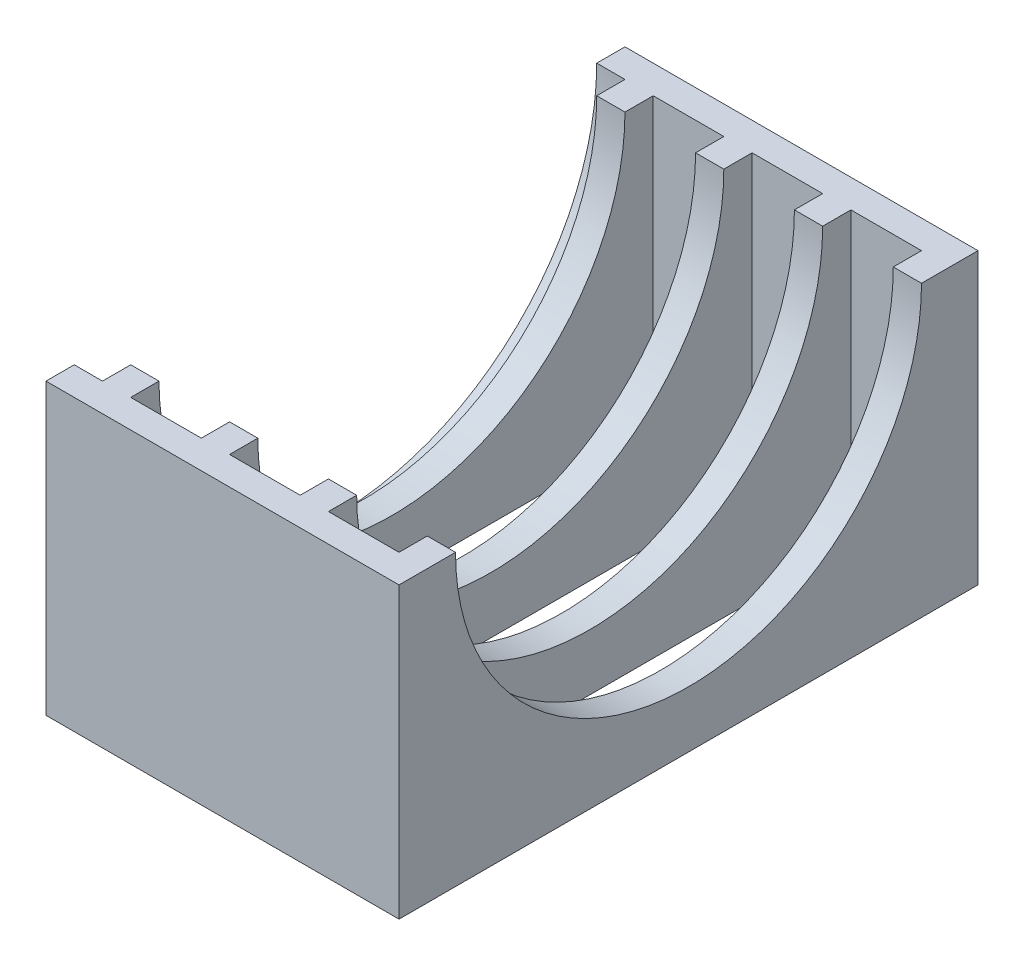
SolidWorks part; units mm, degrees
ref_plane "前视基准面" through (0, 0, 0) normal (0, 0, 1) x (1, 0, 0)
ref_plane "上视基准面" through (0, 0, 0) normal (0, 1, 0) x (1, 0, 0)
ref_plane "右视基准面" through (0, 0, 0) normal (1, 0, 0) x (0, 0, -1)
sketch "草图1" plane through (0, 0, 0) normal (0, 1, 0) x (1, 0, 0)
  line L1 (0, 0) -> (25, 0)
  line L2 (0, 0) -> (0, 41)
  line L3 (0, 41) -> (25, 41)
  line L4 (25, 0) -> (25, 41)
  dimension "D1" = 41
  dimension "D2" = 25
extrude "基座" add sketch "草图1" along normal blind 2
sketch "草图5" plane through (0, 2, 0) normal (0, 1, 0) x (1, 0, 0)
  line L0 (25, 0) -> (25, 41) construction
  line L1 (0, 41) -> (25, 41)
  line L2 (0, 41) -> (0, 39)
  line L3 (0, 39) -> (25, 39)
  line L4 (25, 41) -> (25, 39)
  line L6 (0, 0) -> (25, 0)
  line L7 (0, 0) -> (0, 2)
  line L8 (0, 2) -> (25, 2)
  line L9 (25, 0) -> (25, 2)
  dimension "D1" = 2
  dimension "D2" = 2
extrude "加固" add sketch "草图5" along normal blind 18.5
sketch "草图7" plane through (0, 2, 0) normal (0, 1, 0) x (1, 0, 0)
  line L0 (4, 41) -> (4, 0)
  line L1 (25, 41) -> (0, 41) construction
  line L2 (9, 41) -> (9, -0.7416)
  line L3 (0, 39) -> (0, 2) construction
  line L4 (11, 41) -> (11, 0)
  line L5 (16, 0) -> (16, 41)
  line L6 (0, 0) -> (25, 0) construction
  line L7 (18, 41) -> (18, 0)
  line L8 (23, 41) -> (23, 0)
  line M7 (0, 2) -> (25, 2)
  line M8 (25, 2) -> (25, 39)
  line M9 (25, 39) -> (0, 39)
  line M10 (0, 39) -> (0, 2)
  dimension "D1" = 4
  dimension "D2" = 5
  dimension "D3" = 2
  dimension "D4" = 5
  dimension "D5" = 2
  dimension "D6" = 5
extrude "支架" add sketch "草图7" along normal blind 18.5 contours L0 M9 M10 M7 | L4 L2 M9 M7 | L7 L5 M9 M7 | L8 M9 M7 M8
sketch "草图8" plane through (0, 0, 0) normal (-1, 0, 0) x (0, 0, 1)
  line L0 (-41, 20.5) -> (0, 20.5) construction
  circle A0 centre (-20.5, 20.5) radius 18.5
  dimension "D1" = 37
extrude "开口（大）" cut sketch "草图8" against normal blind 2
sketch "草图9" plane through (25, 0, 0) normal (1, 0, 0) x (0, 0, -1)
  line L0 (0, 20.5) -> (41, 20.5) construction
  circle A0 centre (20.5, 20.5) radius 16.5
  dimension "D1" = 33
extrude "开口（小）" cut sketch "草图9" against normal blind 23
sketch "草图10" plane through (0, 2, 0) normal (0, 1, 0) x (1, 0, 0)
  line L1 (4, 39) -> (9, 39)
  line L2 (4, 39) -> (4, 2)
  line L3 (4, 2) -> (9, 2)
  line L4 (9, 39) -> (9, 2)
  line L5 (11, 39) -> (16, 39)
  line L6 (11, 39) -> (11, 2)
  line L7 (11, 2) -> (16, 2)
  line L8 (16, 39) -> (16, 2)
  line L9 (18, 39) -> (23, 39)
  line L10 (18, 39) -> (18, 2)
  line L11 (18, 2) -> (23, 2)
  line L12 (23, 39) -> (23, 2)
extrude "散热口" cut sketch "草图10" against normal blind 2
